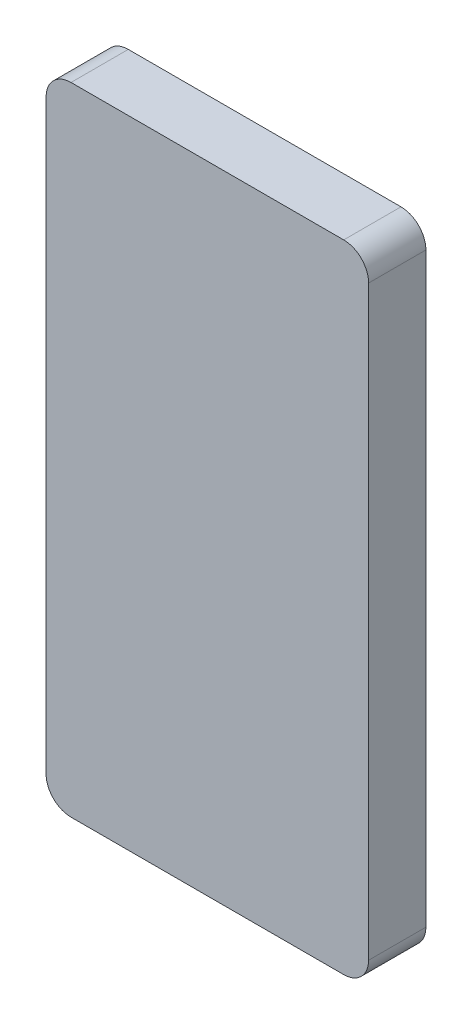
SolidWorks part; units mm, degrees
ref_plane "Front" through (0, 0, 0) normal (0, 0, 1) x (1, 0, 0)
ref_plane "Top" through (0, 0, 0) normal (0, 1, 0) x (1, 0, 0)
ref_plane "Right" through (0, 0, 0) normal (1, 0, 0) x (0, 0, -1)
sketch "Sketch1" plane through (0, 0, 0) normal (0, 0, 1) x (1, 0, 0)
  line L1 (-32.893, -64.897) -> (32.893, -64.897)
  line L2 (-32.893, -64.897) -> (-32.893, 64.897)
  line L3 (-32.893, 64.897) -> (32.893, 64.897)
  line L4 (32.893, -64.897) -> (32.893, 64.897)
  line L5 (-32.893, -64.897) -> (32.893, 64.897) construction
  line L6 (-32.893, 64.897) -> (32.893, -64.897) construction
  point P0 (0, 0)
  dimension "D1" = 129.794
  dimension "D2" = 65.786
extrude "Boss-Extrude1" add sketch "Sketch1" along normal blind 11.684
fillet "Fillet1" radius 5.08 4 edges at (-32.893, -64.897, 5.842) (32.893, -64.897, 5.842) (-32.893, 64.897, 5.842) (32.893, 64.897, 5.842)
